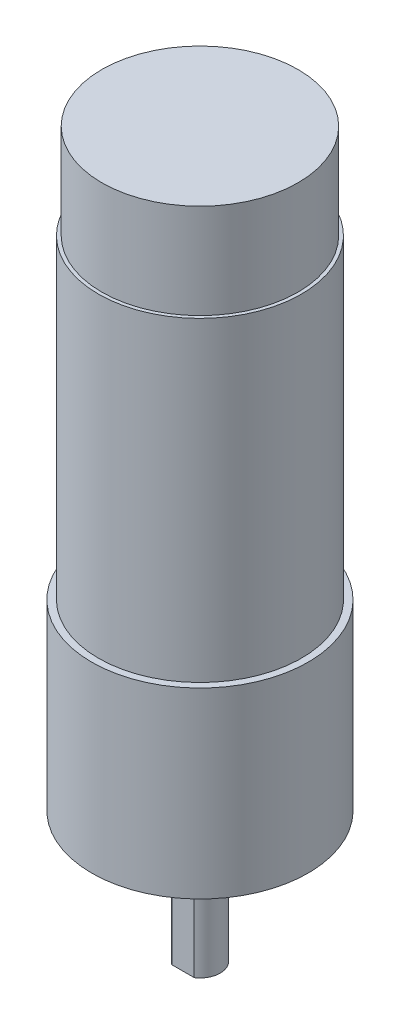
SolidWorks part; units mm, degrees
ref_plane "Plan de face" through (0, 0, 0) normal (0, 0, 1) x (1, 0, 0)
ref_plane "Plan de dessus" through (0, 0, 0) normal (0, 1, 0) x (1, 0, 0)
ref_plane "Plan de droite" through (0, 0, 0) normal (1, 0, 0) x (0, 0, -1)
sketch "Esquisse1" plane through (0, 0, 0) normal (0, 1, 0) x (1, 0, 0)
  circle A0 centre (0, 0) radius 16
  dimension "D1" = 32
extrude "Extrusion1" add sketch "Esquisse1" along normal blind 27
sketch "Esquisse2" plane through (0, 0, 0) normal (0, -1, 0) x (1, 0, 0)
  line L0 (-9, 4.3589) -> (-9, -4.3589)
  line L2 (9, 4.3589) -> (9, -4.3589)
  arc A0 (9, -4.3589) -> (-9, -4.3589) centre (0, 0) cw
  arc A1 (-9, 4.3589) -> (9, 4.3589) centre (0, 0) cw
  dimension "D1" = 9
  dimension "D5" = 10
  dimension "D3" = 10
  dimension "D2" = 18
extrude "Extrusion2" add sketch "Esquisse2" along normal blind 3
sketch "Esquisse3" plane through (0, -3, 0) normal (0, -1, 0) x (1, 0, 0)
  circle A0 centre (0, 0) radius 3
  dimension "D1" = 6
extrude "Extrusion3" add sketch "Esquisse3" along normal blind 16.3
sketch "Esquisse4" plane through (0, -19.3, 0) normal (0, -1, 0) x (1, 0, 0)
  line L0 (0, 0) -> (3, 0) construction
  line L1 (-1.6583, 2.5) -> (1.6583, 2.5)
  circle A0 centre (0, 0) radius 3 construction
  arc A1 (-1.6583, 2.5) -> (1.6583, 2.5) centre (0, 0) cw
  circle M1 centre (0, 0) radius 3
  dimension "D1" = 2.5
extrude "Enlèv. mat.-Extru.1" cut sketch "Esquisse4" against normal blind 12 contours L1 M1
sketch "Esquisse5" plane through (0, 27, 0) normal (0, 1, 0) x (-1, 0, 0)
  circle A0 centre (0, 0) radius 15
  dimension "D1" = 30
extrude "Extrusion4" add sketch "Esquisse5" along normal blind 46.6
sketch "Esquisse6" plane through (0, 0, 0) normal (0, -1, 0) x (1, 0, 0)
  line L0 (-16, 0) -> (16, 0) construction
  line L1 (0, 0) -> (11.3137, 11.3137) construction
  line L2 (0, 16) -> (0, -16) construction
  circle A0 centre (0, 0) radius 16 construction
  circle A1 centre (9.1924, 9.1924) radius 1.5
  circle A2 centre (-9.1924, 9.1924) radius 1.5
  circle A3 centre (9.1924, -9.1924) radius 1.5
  circle A4 centre (-9.1924, -9.1924) radius 1.5
  dimension "D3" = 3
  dimension "D1" = 45
  dimension "D2" = 13
extrude "Enlèv. mat.-Extru.2" cut sketch "Esquisse6" against normal blind 5.5
sketch "Esquisse7" plane through (0, 73.6, 0) normal (0, 1, 0) x (-1, 0, 0)
  circle A0 centre (0, 0) radius 14.5
  dimension "D1" = 29
extrude "Extrusion5" add sketch "Esquisse7" along normal blind 14
